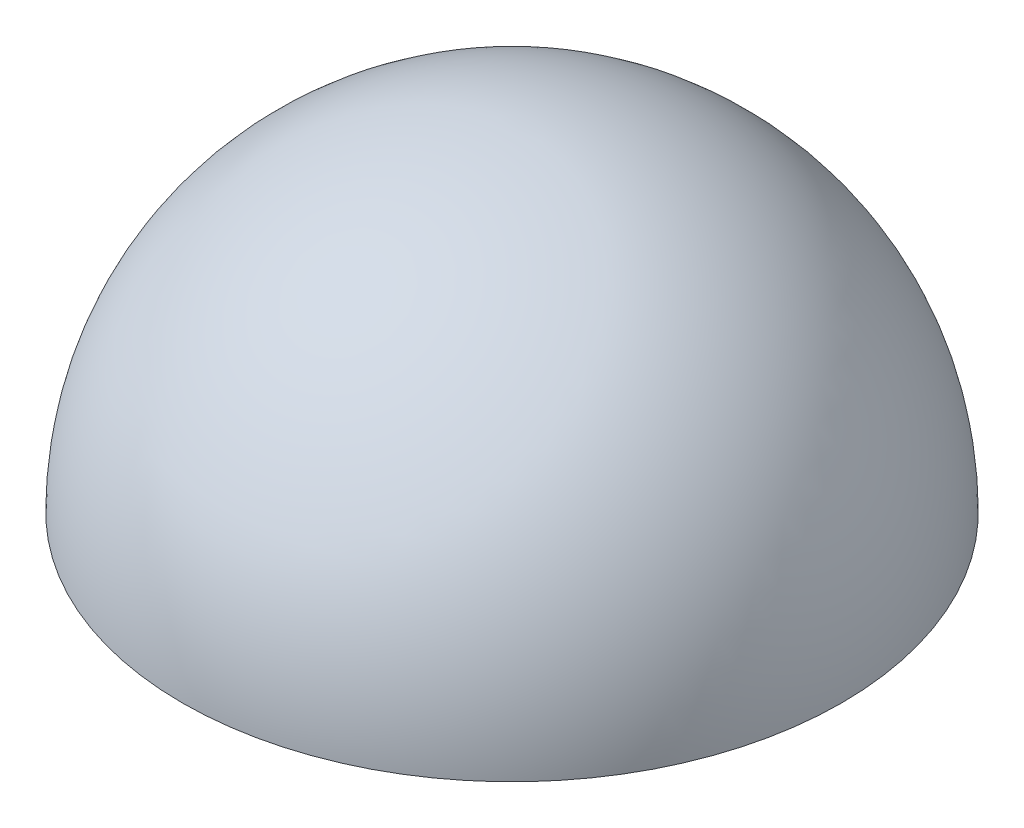
SolidWorks part; units mm, degrees
material "玻璃"
ref_plane "前视基准面" through (0, 0, 0) normal (0, 0, 1) x (1, 0, 0)
ref_plane "上视基准面" through (0, 0, 0) normal (0, 1, 0) x (1, 0, 0)
ref_plane "右视基准面" through (0, 0, 0) normal (1, 0, 0) x (0, 0, -1)
other "Configuration Table"
sketch "草图1" plane through (0, 0, 0) normal (0, 0, 1) x (1, 0, 0)
  line L0 (0, -70) -> (0, 70)
  line L1 (0, 0) -> (-70, 0)
  arc A0 (0, 70) -> (0, -70) centre (0, 0) ccw
  dimension "D1" = 140
revolve "旋转1" add sketch "草图1" angle 360 about L0
